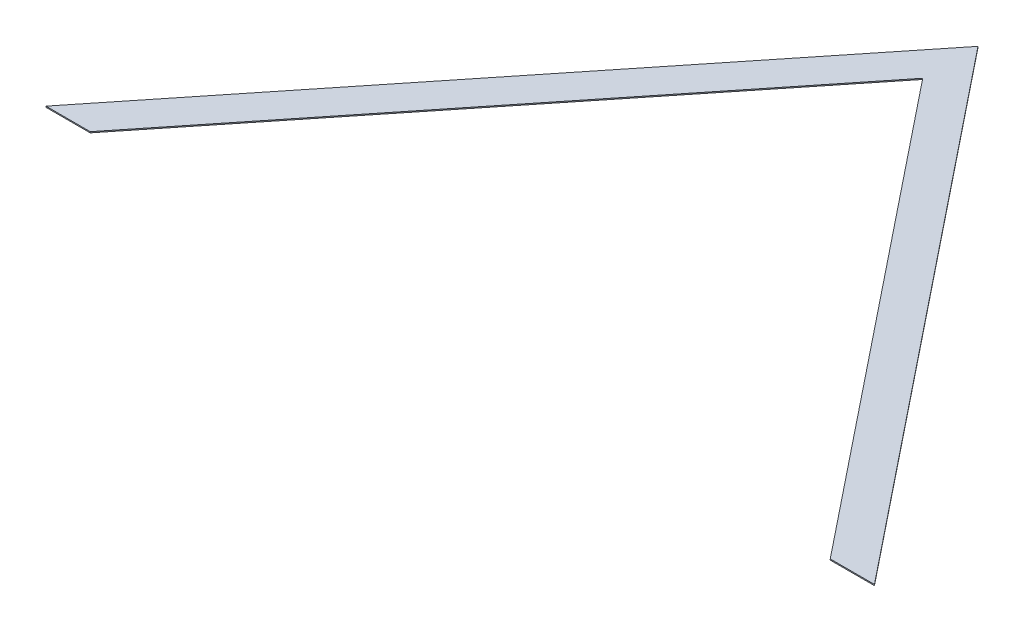
SolidWorks part; units mm, degrees
ref_plane "Front Plane" through (0, 0, 0) normal (0, 0, 1) x (1, 0, 0)
ref_plane "Top Plane" through (0, 0, 0) normal (0, 1, 0) x (1, 0, 0)
ref_plane "Right Plane" through (0, 0, 0) normal (1, 0, 0) x (0, 0, -1)
sketch "Sketch1" plane through (0, 0, 0) normal (0, 1, 0) x (1, 0, 0)
  line L6 (609.6, 0) -> (0, 762)
  line L7 (0, 762) -> (-609.6, 0)
  line L10 (-609.6, 0) -> (-544.5443, 0)
  line L11 (-544.5443, 0) -> (0, 680.6803)
  line L12 (0, 680.6803) -> (544.5443, 0)
  line L13 (544.5443, 0) -> (609.6, 0)
  dimension "D2" = 1219.2
  dimension "D3" = 762
  dimension "D1" = 50.8
extrude "Boss-Extrude1" add sketch "Sketch1" along normal blind 1.5875
